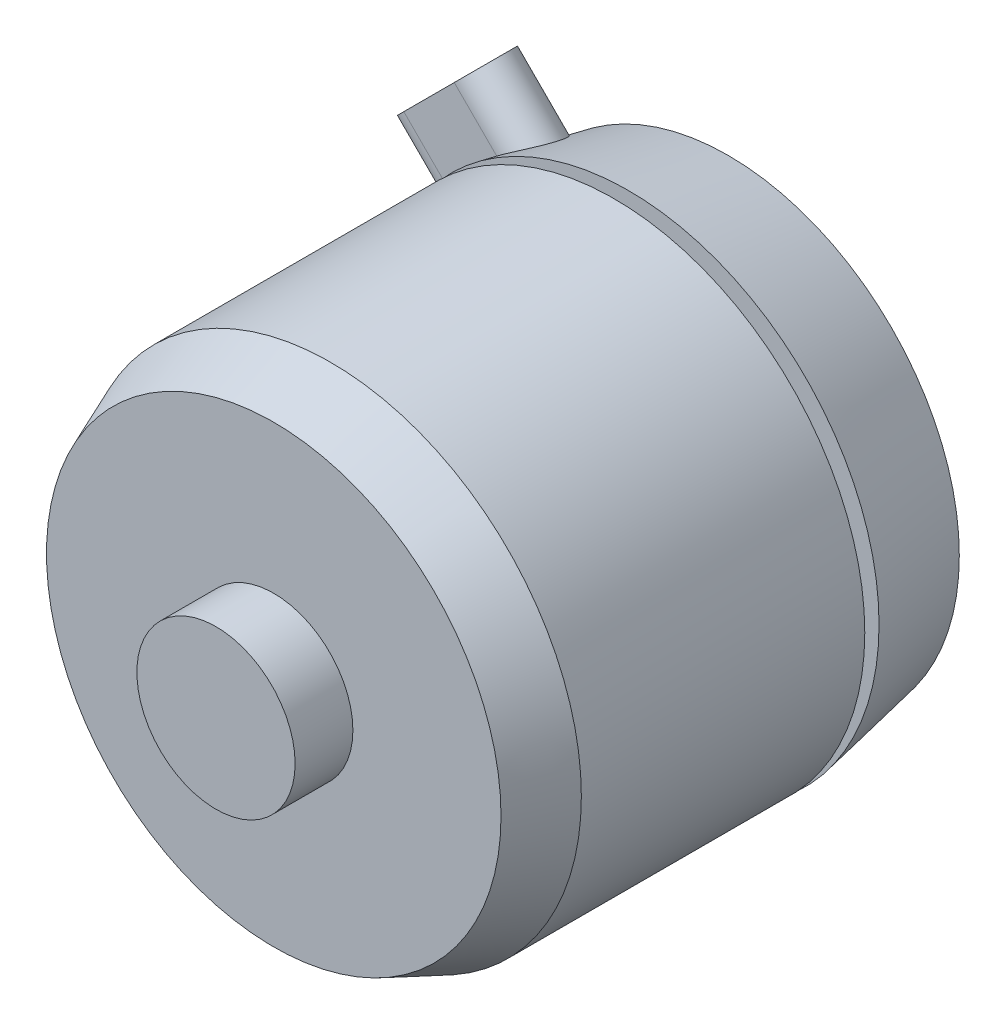
SolidWorks part; units mm, degrees
material "Turnigy Aerodrive D3536/5 1450"
ref_plane "Front Plane" through (0, 0, 0) normal (0, 0, 1) x (1, 0, 0)
ref_plane "Top Plane" through (0, 0, 0) normal (0, 1, 0) x (1, 0, 0)
ref_plane "Right Plane" through (0, 0, 0) normal (1, 0, 0) x (0, 0, -1)
sketch "Sketch1" plane through (0, 0, 0) normal (1, 0, 0) x (0, 0, -1)
  line L0 (0, 0) -> (0, 5.5499)
  line L1 (0, 5.5499) -> (4.0513, 5.5499)
  line L2 (4.0513, 5.5499) -> (4.0513, 15.94)
  line L3 (4.0513, 15.94) -> (8.0513, 17.575)
  line L4 (35.9313, 16.205) -> (35.9313, 4.7308)
  line L5 (-1000, 0) -> (49000, 0) construction
  line L6 (28.9313, 17.575) -> (35.9313, 16.205)
  line L7 (28.9313, 17.575) -> (28.9313, 6.0198)
  line L8 (0, 0) -> (37.4807, 0)
  line L9 (28.9313, 6.0198) -> (27.9313, 6.0198)
  line L10 (27.9313, 6.0198) -> (27.9313, 17.575)
  line L11 (8.0513, 17.575) -> (27.9313, 17.575)
  line L12 (36.5155, 4.7307) -> (36.5155, 2.4511)
  line L13 (36.5155, 4.7307) -> (35.9313, 4.7308)
  line L14 (36.5155, 2.4511) -> (37.4807, 2.4511)
  line L15 (37.4807, 2.4511) -> (37.4807, 0)
  dimension "D1" = 31.88
  dimension "D2" = 17.575
  dimension "D3" = 7
  dimension "D4" = 5.5499
  dimension "D5" = 4.0513
  dimension "D6" = 1
  dimension "D7" = 15.94
  dimension "D8" = 4
  dimension "D9" = 16.205
  dimension "D10" = 4.7307
  dimension "D11" = 2.4511
  dimension "D12" = 0.5842
  dimension "D13" = 1.5494
revolve "Revolve1" add sketch "Sketch1" angle 360 about L5
sketch "Sketch2" plane through (0, 0, -35.9313) normal (0, 0, -1) x (-1, 0, 0)
  line L0 (-12.57, 0) -> (0, 0) construction
  line L1 (0, 0) -> (0, 9.545) construction
  line L2 (-703.4251, 0) -> (49296.5749, 0) construction
  circle A0 centre (-12.57, 0) radius 1.29
  circle A1 centre (0, 9.545) radius 1.29
  circle A2 centre (12.57, 0) radius 1.29
  circle A3 centre (0, -9.545) radius 1.29
  dimension "D4" = 2.58
  dimension "D5" = 22.56
  dimension "D6" = 16.51
  dimension "D2" = 90
  dimension "D1" = 2
extrude "Cut-Extrude1" cut sketch "Sketch2" against normal blind 7
ref_plane "Plane1" through (-12.4274, 12.4274, 0) normal (-0.7071, 0.7071, 0) x (0, 0, -1)
sketch "Sketch3" plane through (-12.4274, 12.4274, 0) normal (-0.7071, 0.7071, 0) x (0, 0, -1)
  line L0 (32.0578, 2.5019) -> (32.0578, -2.5019) construction
  line L1 (34.0517, 2.5019) -> (34.0517, -2.5019)
  line L2 (30.0639, 2.5019) -> (30.0639, -2.5019)
  line L5 (35.9313, -16.205) -> (35.9313, 16.205) construction
  arc A0 (34.0517, 2.5019) -> (30.0639, 2.5019) centre (32.0578, 2.5019) ccw
  arc A1 (30.0639, -2.5019) -> (34.0517, -2.5019) centre (32.0578, -2.5019) ccw
  point P2 (32.0578, 0)
  dimension "D2" = 8.9916
  dimension "D1" = 3.9878
  dimension "D3" = 1.8796
extrude "Boss-Extrude1" add sketch "Sketch3" along normal mid plane 7.62
